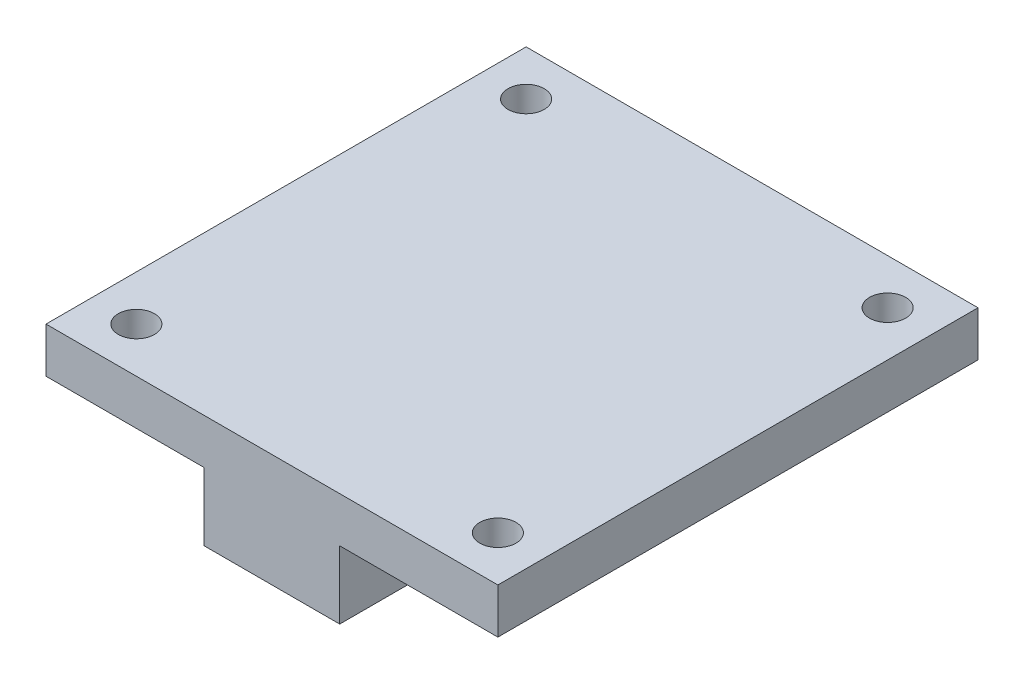
SolidWorks part; units mm, degrees
ref_plane "Plan de face" through (0, 0, 0) normal (0, 0, 1) x (1, 0, 0)
ref_plane "Plan de dessus" through (0, 0, 0) normal (0, 1, 0) x (1, 0, 0)
ref_plane "Plan de droite" through (0, 0, 0) normal (1, 0, 0) x (0, 0, -1)
sketch "Esquisse1" plane through (0, 0, 0) normal (0, 0, -1) x (1, 0, 0)
  line L0 (-1.3845, -46.2204) -> (38.6155, -46.2204)
  line L1 (38.6155, -46.2204) -> (38.6155, -42.2204)
  line L2 (38.6155, -42.2204) -> (24.6155, -42.2204)
  line L3 (24.6155, -42.2204) -> (24.6155, -36.2204)
  line L4 (24.6155, -36.2204) -> (12.6155, -36.2204)
  line L5 (12.6155, -36.2204) -> (12.6155, -42.2204)
  line L6 (12.6155, -42.2204) -> (-1.3845, -42.2204)
  line L7 (-1.3845, -42.2204) -> (-1.3845, -46.2204)
  point P8 (0, 0)
  dimension "D1" = 40
  dimension "D2" = 4
  dimension "D3" = 14
  dimension "D4" = 6
  dimension "D5" = 12
  dimension "D6" = 6
extrude "Boss.-Extru.1" add sketch "Esquisse1" along normal blind 42.5
hole_wizard "Dégagement M31" positions "Esquisse4" profile "Esquisse5" hole size "M3" standard "Din" end condition through all
sketch "Esquisse4" plane through (24.6155, 0, 0) normal (1, 0, 0) x (0, 0, -1)
  line L0 (0, 39.2204) -> (42.5, 39.2204) construction
  line L1 (0, 42.2204) -> (0, 36.2204) construction
  line L2 (42.5, 42.2204) -> (42.5, 36.2204) construction
  point P0 (10, 39.2204)
  point P2 (32.5, 39.2204)
  dimension "D1" = 10
  dimension "D2" = 10
sketch "Esquisse5" plane through (24.6155, 39.2204, -10) normal (0, 1, 0) x (0, 0, -1)
  line L0 (0, 0) -> (0, 26)
  line L1 (0, 26) -> (1.5, 26)
  line L2 (1.5, 26) -> (1.5, 0)
  line L5 (1.5, 0) -> (0, 0)
  line L11 (0, -6.35) -> (0, 107.95) construction
  dimension "Diamètre du perçage jusqu'au prochain" = 3
  dimension "Profondeur du perçage jusqu'au prochain" = 26
hole_wizard "Dégagement M33" positions "Esquisse7" profile "Esquisse8" hole size "M3" standard "Din" end condition through all
sketch "Esquisse7" plane through (0, 42.2204, 0) normal (0, -1, 0) x (-1, 0, 0)
  line L1 (-34.6155, 38.5) -> (-2.6155, 38.5) construction
  line L2 (-34.6155, 38.5) -> (-34.6155, 4) construction
  line L3 (-34.6155, 4) -> (-2.6155, 4) construction
  line L4 (-2.6155, 38.5) -> (-2.6155, 4) construction
  line L5 (-24.6155, 42.5) -> (-12.6155, 42.5) construction
  line L6 (1.3845, 42.5) -> (1.3845, 0) construction
  line L7 (-38.6155, 42.5) -> (-38.6155, 0) construction
  point P0 (3, -59.9463)
  point P1 (-34.6155, 38.5)
  point P3 (-2.6155, 38.5)
  point P5 (-2.6155, 4)
  point P7 (-34.6155, 4)
  dimension "D1" = 4
  dimension "D2" = 4
  dimension "D3" = 4
  dimension "D4" = 4
sketch "Esquisse8" plane through (-3, 42.2204, 59.9463) normal (1, 0, 0) x (0, 0, -1)
  line L0 (0, 0) -> (0, 4)
  line L1 (0, 4) -> (1.6, 4)
  line L2 (1.6, 4) -> (1.6, 0)
  line L5 (1.6, 0) -> (0, 0)
  line L11 (0, -6.35) -> (0, 107.95) construction
  dimension "Diamètre du perçage jusqu'au prochain" = 3.2
  dimension "Profondeur du perçage jusqu'au prochain" = 4
sketch "Esquisse9" plane through (0, 42.2204, 0) normal (0, -1, 0) x (1, 0, 0)
  line L1 (32.8655, -35.4689) -> (31.1155, -38.5)
  line L2 (31.1155, -38.5) -> (32.8655, -41.5311)
  line L3 (32.8655, -41.5311) -> (36.3655, -41.5311)
  line L4 (36.3655, -41.5311) -> (38.1155, -38.5)
  line L5 (38.1155, -38.5) -> (36.3655, -35.4689)
  line L6 (36.3655, -35.4689) -> (32.8655, -35.4689)
  line L7 (4.3655, -35.4689) -> (0.8655, -35.4689)
  line L8 (0.8655, -35.4689) -> (-0.8845, -38.5)
  line L9 (-0.8845, -38.5) -> (0.8655, -41.5311)
  line L10 (0.8655, -41.5311) -> (4.3655, -41.5311)
  line L11 (4.3655, -41.5311) -> (6.1155, -38.5)
  line L12 (6.1155, -38.5) -> (4.3655, -35.4689)
  line L13 (32.8655, -0.9689) -> (31.1155, -4)
  line L14 (31.1155, -4) -> (32.8655, -7.0311)
  line L15 (32.8655, -7.0311) -> (36.3655, -7.0311)
  line L16 (36.3655, -7.0311) -> (38.1155, -4)
  line L17 (38.1155, -4) -> (36.3655, -0.9689)
  line L18 (36.3655, -0.9689) -> (32.8655, -0.9689)
  line L19 (4.3655, -0.9689) -> (0.8655, -0.9689)
  line L20 (0.8655, -0.9689) -> (-0.8845, -4)
  line L21 (-0.8845, -4) -> (0.8655, -7.0311)
  line L22 (0.8655, -7.0311) -> (4.3655, -7.0311)
  line L23 (4.3655, -7.0311) -> (6.1155, -4)
  line L24 (6.1155, -4) -> (4.3655, -0.9689)
  circle A0 centre (34.6155, -38.5) radius 3.0311 construction
  circle A1 centre (2.6155, -38.5) radius 3.0311 construction
  circle A2 centre (34.6155, -4) radius 3.0311 construction
  circle A3 centre (2.6155, -4) radius 3.0311 construction
  dimension "D1" = 3.5
extrude "Enlèv. mat.-Extru.1" cut sketch "Esquisse9" against normal blind 1
